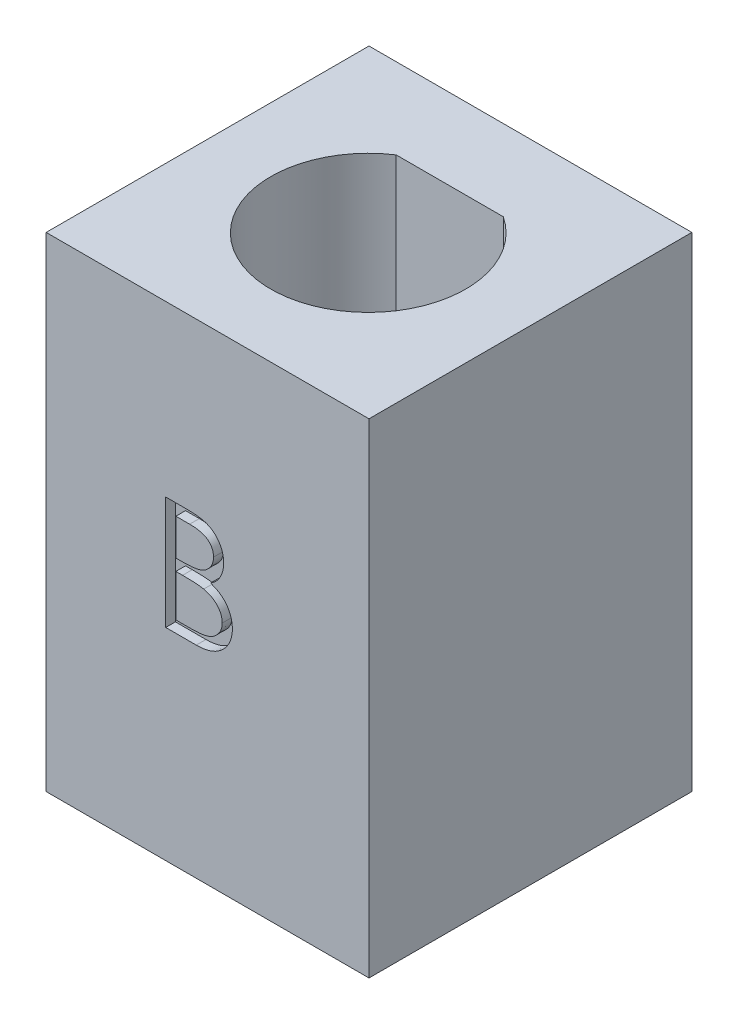
SolidWorks part; units mm, degrees
ref_plane "Front Plane" through (0, 0, 0) normal (0, 0, 1) x (1, 0, 0)
ref_plane "Top Plane" through (0, 0, 0) normal (0, 1, 0) x (1, 0, 0)
ref_plane "Right Plane" through (0, 0, 0) normal (1, 0, 0) x (0, 0, -1)
sketch "Sketch1" plane through (0, 0, 0) normal (0, 1, 0) x (1, 0, 0)
  line L0 (-1.6583, 2.5) -> (1.6583, 2.5)
  line L2 (-5, 5) -> (5, 5)
  line L3 (-5, 5) -> (-5, -5)
  line L4 (-5, -5) -> (5, -5)
  line L5 (5, 5) -> (5, -5)
  arc A1 (-1.6583, 2.5) -> (1.6583, 2.5) centre (0, -0.024) ccw
  point P3 (0, 2.5)
extrude "Boss-Extrude1" add sketch "Sketch1" along normal blind 15
sketch "Sketch2" plane through (0, 0, 5) normal (0, 0, 1) x (1, 0, 0)
  text T0 "B"
extrude "Cut-Extrude1" cut sketch "Sketch2" against normal blind 0.3
